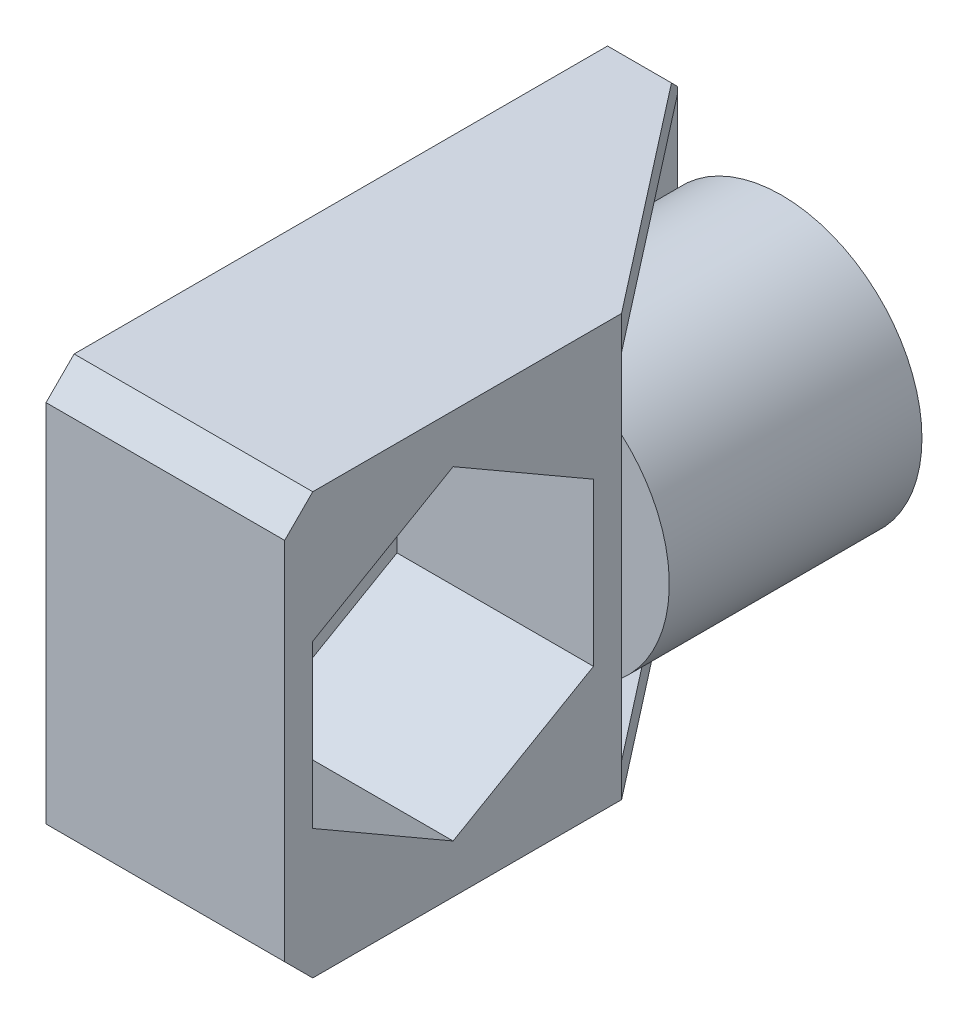
SolidWorks part; units mm, degrees
ref_plane "Alzado" through (0, 0, 0) normal (0, 0, 1) x (1, 0, 0)
ref_plane "Planta" through (0, 0, 0) normal (0, 1, 0) x (1, 0, 0)
ref_plane "Vista lateral" through (0, 0, 0) normal (1, 0, 0) x (0, 0, -1)
sketch "Croquis1" plane through (0, 0, 0) normal (0, 0, 1) x (1, 0, 0)
  line L0 (0, 0) -> (9856.1717, 0) construction
  line L1 (0, 0) -> (0, 9856.1717) construction
  line L2 (4, -13.8382) -> (4, 9842.3335) construction
  line L3 (10, -15.0775) -> (10, 9841.0942) construction
  line L4 (-4, -13.8382) -> (-4, 9842.3335) construction
  line L5 (-10, -15.0775) -> (-10, 9841.0942) construction
  line L6 (-5.2, 1.704) -> (-5.2, 50001.704) construction
  line L7 (-8.2, -11.9793) -> (-8.2, 49988.0207) construction
  line L8 (-26.2702, -15) -> (49973.7298, -15) construction
  line L9 (0, 0) -> (7.8369, 9.3397) construction
  line L10 (1.9284, 2.2981) -> (3.2139, 3.8302) construction
  line L11 (0, 0) -> (6.4279, -7.6604) construction
  line L13 (1.9284, -2.2981) -> (3.2139, -3.8302) construction
  line L14 (-4.3301, 2.5) -> (-5.2, 2.5)
  line L15 (-5.2, 2.5) -> (-5.2, -2.5)
  line L16 (-5.2, -2.5) -> (-4.3301, -2.5)
  circle A0 centre (0, 0) radius 3 construction
  arc A1 (1.9284, 2.2981) -> (1.9284, -2.2981) centre (0, 0) ccw
  arc A2 (3.2139, 3.8302) -> (-4.3301, 2.5) centre (0, 0) ccw
  arc A4 (-4.3301, -2.5) -> (3.2139, -3.8302) centre (0, 0) ccw
  arc A5 (3.2139, -3.8302) -> (3.2139, 3.8302) centre (0, 0) ccw
  arc A6 (1.9284, 2.2981) -> (1.9284, -2.2981) centre (0, 0) cw
  point P29 (-5.2, 0)
  point P33 (2.1028, 2.1396)
  point P34 (2.153, -2.0891)
  point P36 (0.1801, 0)
  dimension "D3" = 6
  dimension "D6" = 15
  dimension "D7" = 50
  dimension "D8" = 2
  dimension "D9" = 5
  dimension "D1" = 4
  dimension "D2" = 10
  dimension "D4" = 1.2
  dimension "D5" = 3
extrude "Saliente-Extruir1" add sketch "Croquis1" along normal blind 9
sketch "Croquis3" plane through (-5.2, 0, 0) normal (-1, 0, 0) x (0, 0, 1)
  line L0 (0, 0) -> (0, 49942.1244) construction
  line L1 (0, 7.5) -> (21, 7.5)
  line L2 (0, 7.5) -> (0, -7.5)
  line L3 (0, -7.5) -> (21, -7.5)
  line L4 (21, 7.5) -> (21, -7.5)
  line L5 (0, 7.5) -> (21, -7.5) construction
  line L6 (0, -7.5) -> (21, 7.5) construction
  line L7 (0, 0) -> (50000, 0) construction
  point P4 (10.5, 0)
  dimension "D1" = 21
  dimension "D2" = 15
extrude "Saliente-Extruir2" add sketch "Croquis3" against normal blind 1.5
sketch "Croquis4" plane through (-5.2, 0, 0) normal (-1, 0, 0) x (0, 0, 1)
  line L0 (0, 0) -> (50000, 0) construction
  circle A0 centre (15, 0) radius 3
  point P9 (0, 0)
  dimension "D1" = 6
  dimension "D2" = 15
extrude "Cortar-Extruir1" cut sketch "Croquis4" against normal through all
sketch "Croquis5" plane through (-3.7, 0, 0) normal (1, 0, 0) x (0, 0, -1)
  line L1 (-21, 7.5) -> (-9, 7.5)
  line L2 (-21, 7.5) -> (-21, -7.5)
  line L3 (-21, -7.5) -> (-9, -7.5)
  line L4 (-9, 7.5) -> (-9, -7.5)
  line L5 (-21, 7.5) -> (-9, -7.5) construction
  line L6 (-21, -7.5) -> (-9, 7.5) construction
  line L8 (0, 0) -> (-50000, 0) construction
  point P4 (-15, 0)
extrude "Saliente-Extruir3" add sketch "Croquis5" along normal blind 7
sketch "Croquis7" plane through (3.3, 0, 0) normal (1, 0, 0) x (0, 0, -1)
  line L1 (-10, -2.8868) -> (-10, 2.8868)
  line L2 (-10, 2.8868) -> (-15, 5.7735)
  line L3 (-15, 5.7735) -> (-20, 2.8868)
  line L4 (-20, 2.8868) -> (-20, -2.8868)
  line L5 (-20, -2.8868) -> (-15, -5.7735)
  line L6 (-15, -5.7735) -> (-10, -2.8868)
  circle A0 centre (-15, 0) radius 5 construction
  dimension "D1" = 10
extrude "Cortar-Extruir2" cut sketch "Croquis7" against normal up to surface (7 mm away) up to face at (-3.7, 5.4315, 4.5)
fillet "Redondeo1" [suppressed] radius 1
chamfer "Chaflán1" distance 0.5 angle 45 1 edges at (3, 0, 0)
sketch "Croquis8" plane through (0, 7.5, 0) normal (0, 1, 0) x (1, 0, 0)
  line L0 (-3.7, 0) -> (3.3, -9)
  line L1 (3.3, -9) -> (-3.7, -9)
  line L2 (-3.7, -9) -> (-3.7, 0)
extrude "Saliente-Extruir4" add sketch "Croquis8" against normal blind 1.2
mirror "Simetría1" about plane through (0, 0, 0) normal (0, 1, 0) of "Saliente-Extruir4"
chamfer "Chaflán2" distance 1 angle 45 4 edges at (-0.95, 7.5, 21) (-0.95, -7.5, 21) (-4.45, -7.5, 0) (-4.45, 7.5, 0)
